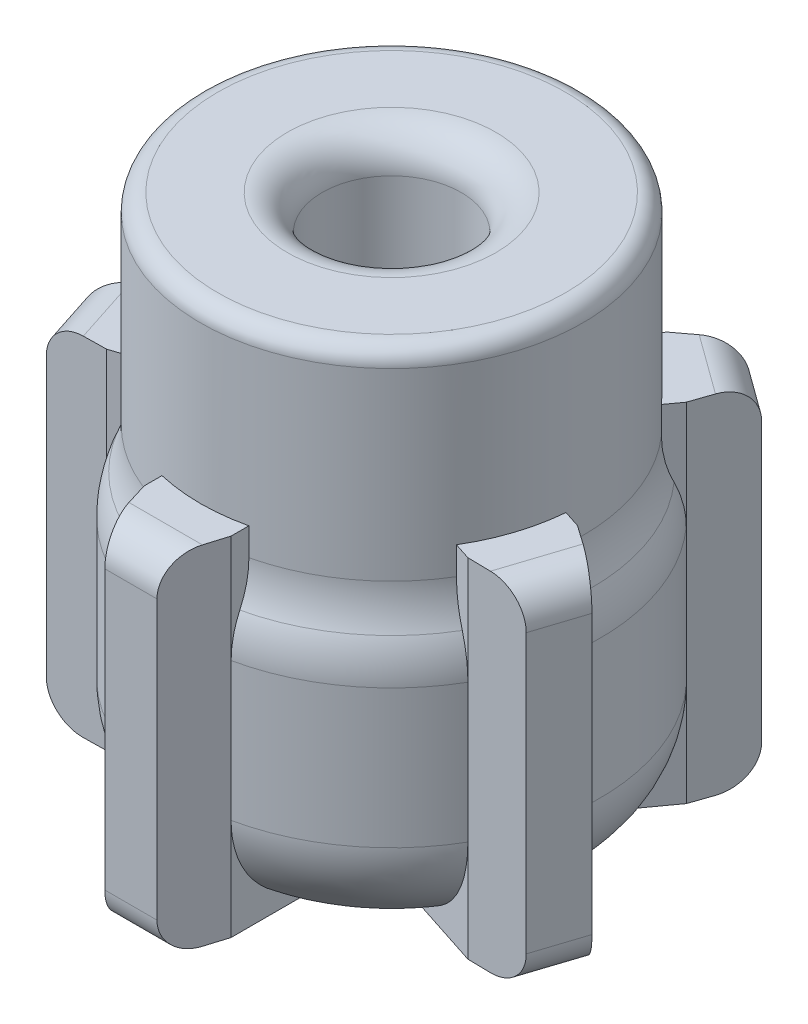
SolidWorks part; units mm, degrees
ref_plane "Front Plane" through (0, 0, 0) normal (0, 0, 1) x (1, 0, 0)
ref_plane "Top Plane" through (0, 0, 0) normal (0, 1, 0) x (1, 0, 0)
ref_plane "Right Plane" through (0, 0, 0) normal (1, 0, 0) x (0, 0, -1)
sketch "Sketch1" plane through (0, 0, 0) normal (0, 0, 1) x (1, 0, 0)
  line L0 (0, 30) -> (0, 0)
  line L2 (-11, 18.4097) -> (-11, 29)
  line L3 (-10, 30) -> (0, 30)
  line L4 (-12, 13.798) -> (-12, 5.8351)
  line L5 (0, 0) -> (-6.1649, 0)
  arc A0 (-12, 13.798) -> (-11.5092, 16.0612) centre (-6.536, 13.798) cw
  arc A1 (-11.5092, 16.0612) -> (-11, 18.4097) centre (-16.6699, 18.4097) ccw
  arc A2 (-11, 29) -> (-10, 30) centre (-10, 29) cw
  arc A3 (-6.1649, 0) -> (-12, 5.8351) centre (-6.1649, 5.8351) cw
  point P13 (-11, 30)
  dimension "D1" = 12
  dimension "D4" = 1
  dimension "D2" = 11
  dimension "D3" = 30
revolve "Revolve1" add sketch "Sketch1" angle 360 about L0
sketch "Sketch2" plane through (0, 0, 0) normal (0, -1, 0) x (1, 0, 0)
  line L0 (0, 11.9267) -> (0, 12.0733) construction
  line L7 (-1.5, 15) -> (1.5, 15)
  line L8 (1.5, 15) -> (2.5, 11.7367)
  line L9 (2.5, 11.7367) -> (2.5, 5.6353)
  line L10 (-2.5, 11.7367) -> (-2.5, 5.6353)
  line L11 (-1.5, 15) -> (-2.5, 11.7367)
  line L12 (-2.5, 5.6353) -> (2.5, 5.6353)
  line L13 (10.3897, 6.0045) -> (4.5869, 4.119)
  line L14 (13.8023, 6.0618) -> (10.3897, 6.0045)
  line L15 (13.8023, 6.0618) -> (14.7294, 3.2087)
  line L16 (14.7294, 3.2087) -> (11.9348, 1.2492)
  line L17 (11.9348, 1.2492) -> (6.132, -0.6362)
  line L18 (4.5869, 4.119) -> (6.132, -0.6362)
  line L19 (8.9212, -8.0257) -> (5.3349, -3.0896)
  line L20 (10.0303, -11.2536) -> (8.9212, -8.0257)
  line L21 (10.0303, -11.2536) -> (7.6033, -13.0169)
  line L22 (7.6033, -13.0169) -> (4.8761, -10.9646)
  line L23 (4.8761, -10.9646) -> (1.2898, -6.0285)
  line L24 (5.3349, -3.0896) -> (1.2898, -6.0285)
  line L25 (-4.8761, -10.9646) -> (-1.2898, -6.0285)
  line L26 (-7.6033, -13.0169) -> (-4.8761, -10.9646)
  line L27 (-7.6033, -13.0169) -> (-10.0303, -11.2536)
  line L28 (-10.0303, -11.2536) -> (-8.9212, -8.0257)
  line L29 (-8.9212, -8.0257) -> (-5.3349, -3.0896)
  line L30 (-1.2898, -6.0285) -> (-5.3349, -3.0896)
  line L31 (-11.9348, 1.2492) -> (-6.132, -0.6362)
  line L32 (-14.7294, 3.2087) -> (-11.9348, 1.2492)
  line L33 (-14.7294, 3.2087) -> (-13.8023, 6.0618)
  line L34 (-13.8023, 6.0618) -> (-10.3897, 6.0045)
  line L35 (-10.3897, 6.0045) -> (-4.5869, 4.119)
  line L36 (-6.132, -0.6362) -> (-4.5869, 4.119)
  circle A1 centre (0, 0) radius 12 construction
  circle A9 centre (0, 0) radius 6.1649 construction
  point P1 (1.2697, 15)
  point P3 (0, 12)
  point P12 (-14.7903, 24.279)
  point P16 (0, 15)
  dimension "D1" = 3
  dimension "D3" = 3
  dimension "D4" = 5
  dimension "D2" = 5
sketch "Sketch3" plane through (0, 30, 0) normal (0, 1, 0) x (1, 0, 0)
  circle A0 centre (0, 0) radius 4
  dimension "D1" = 8
extrude "Cut-Extrude2" cut sketch "Sketch3" against normal offset from surface (29 mm away) 1 up to face at (-6.1649, 0, 0)
fillet "Fillet2" radius 2 1 edges at (-4, 30, 0)
extrude "Boss-Extrude1" add sketch "Sketch2" against normal blind 20
fillet "Fillet3" radius 2 10 edges at (0, 0, 15) (0, 20, 15) (14.2658, 0, 4.6353) (14.2658, 20, 4.6353) (8.8168, 0, -12.1353) (8.8168, 20, -12.1353) (-8.8168, 0, -12.1353) (-8.8168, 20, -12.1353) (-14.2658, 0, 4.6353) (-14.2658, 20, 4.6353)
